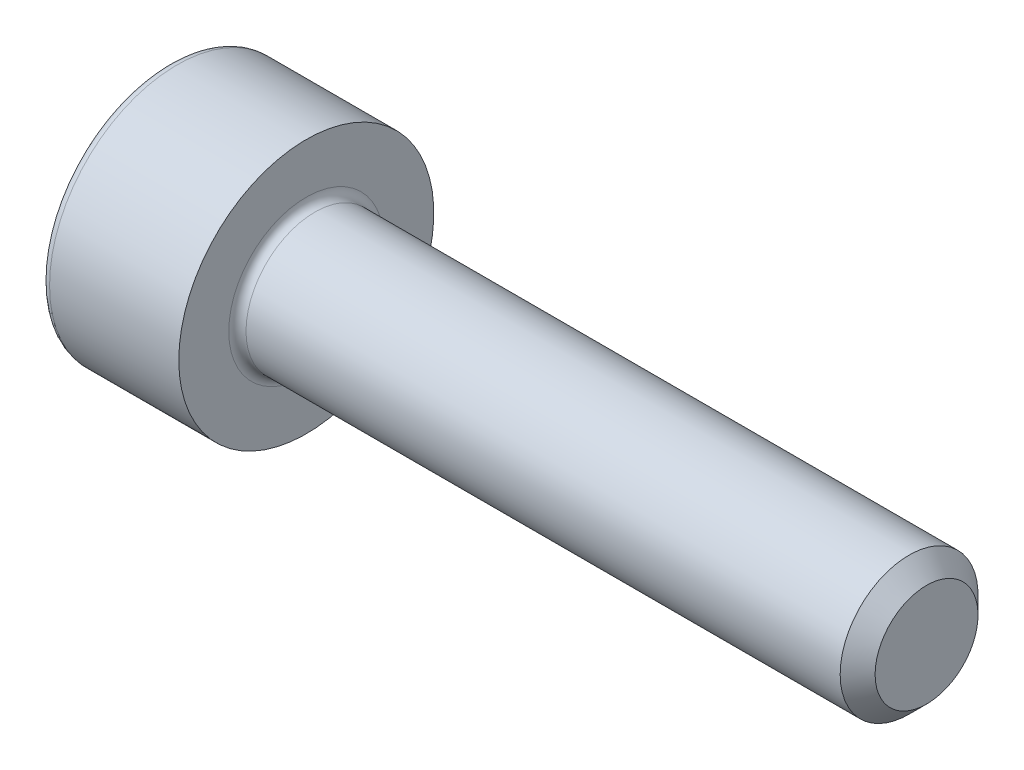
SolidWorks part; units mm, degrees
ref_plane "Front" through (0, 0, 0) normal (0, 0, 1) x (1, 0, 0)
ref_plane "Top" through (0, 0, 0) normal (0, 1, 0) x (1, 0, 0)
ref_plane "Right" through (0, 0, 0) normal (1, 0, 0) x (0, 0, -1)
sketch "Sketch1" plane through (0, 0, 0) normal (0, 0, 1) x (1, 0, 0)
  line L0 (8.7465, 1) -> (0.125, 1)
  line L1 (-2, 1.725) -> (-2, 0)
  line L2 (0, 1.85) -> (-1.875, 1.85)
  line L3 (0, 1.125) -> (0, 1.85)
  line L4 (9, 0.7465) -> (9, 0)
  line L5 (9, 0.7465) -> (8.7465, 1)
  line L6 (-2, 0) -> (0, 0) construction
  line L7 (-2, 0) -> (9, 0)
  arc A0 (-1.875, 1.85) -> (-2, 1.725) centre (-1.875, 1.725) ccw
  arc A1 (0, 1.125) -> (0.125, 1) centre (0.125, 1.125) ccw
  point P12 (0, 1.4875)
  dimension "D5" = 0.125
  dimension "D1" = 2
  dimension "D2" = 3.7
  dimension "D3" = 135
  dimension "D4" = 0.3585
  dimension "D6" = 9
  dimension "D7" = 2
revolve "Revolve1" add sketch "Sketch1" angle 360 about L7
sketch "Sketch2" plane through (-2, 0, 0) normal (-1, 0, 0) x (0, 0, 1)
  line L7 (0.75, 0.433) -> (0, 0.866)
  line L8 (0, 0.866) -> (-0.75, 0.433)
  line L9 (-0.75, 0.433) -> (-0.75, -0.433)
  line L10 (-0.75, -0.433) -> (0, -0.866)
  line L11 (0, -0.866) -> (0.75, -0.433)
  line L12 (0.75, -0.433) -> (0.75, 0.433)
  circle A0 centre (0, 0) radius 0.75 construction
  dimension "D1" = 1.5
extrude "Cut-Extrude1" cut sketch "Sketch2" against normal blind 1.1
